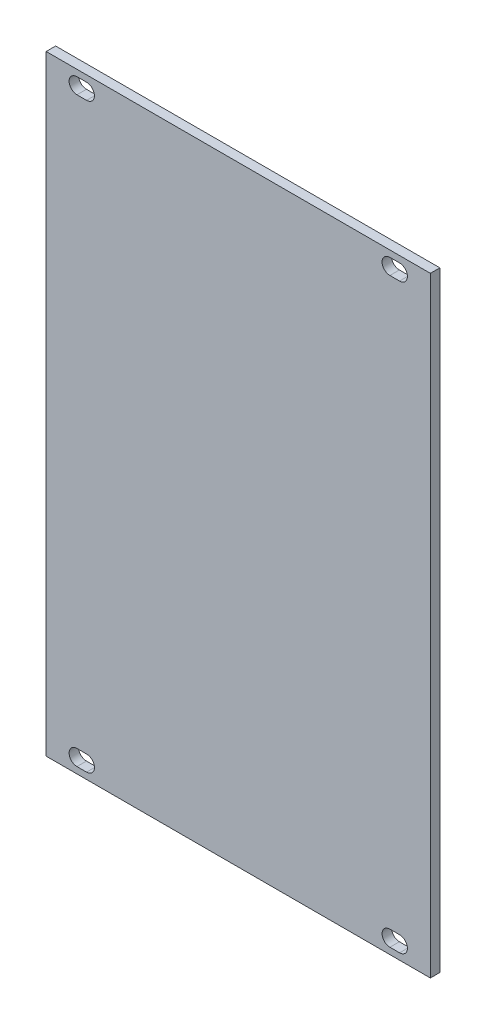
SolidWorks part; units mm, degrees
ref_plane "Front Plane" through (0, 0, 0) normal (0, 0, 1) x (1, 0, 0)
ref_plane "Top Plane" through (0, 0, 0) normal (0, 1, 0) x (1, 0, 0)
ref_plane "Right Plane" through (0, 0, 0) normal (1, 0, 0) x (0, 0, -1)
sketch "Sketch1" plane through (0, 0, 0) normal (0, 0, 1) x (1, 0, 0)
  line L0 (-32.95, 64.25) -> (-32.95, -64.25) construction
  line L1 (-40.45, 64.25) -> (40.45, 64.25)
  line L2 (-40.45, 64.25) -> (-40.45, -64.25)
  line L3 (-40.45, -64.25) -> (40.45, -64.25)
  line L4 (40.45, 64.25) -> (40.45, -64.25)
  line L5 (-40.45, 64.25) -> (40.45, -64.25) construction
  line L6 (-40.45, -64.25) -> (40.45, 64.25) construction
  line L7 (-40.45, 61.25) -> (40.45, 61.25) construction
  line L8 (-40.45, -61.25) -> (40.45, -61.25) construction
  line L9 (-33.966, -61.25) -> (-31.934, -61.25) construction
  line L10 (31.934, 61.25) -> (33.966, 61.25) construction
  line L11 (-33.966, -59.6) -> (-31.934, -59.6)
  line L12 (-33.966, -62.9) -> (-31.934, -62.9)
  line L13 (-33.966, 61.25) -> (-31.934, 61.25) construction
  line L14 (-33.966, 62.9) -> (-31.934, 62.9)
  line L15 (-33.966, 59.6) -> (-31.934, 59.6)
  line L16 (31.934, 62.9) -> (33.966, 62.9)
  line L17 (31.934, 59.6) -> (33.966, 59.6)
  line L18 (31.934, -61.25) -> (33.966, -61.25) construction
  line L19 (31.934, -59.6) -> (33.966, -59.6)
  line L20 (31.934, -62.9) -> (33.966, -62.9)
  line L21 (32.95, 64.25) -> (32.95, -64.25) construction
  arc A0 (-33.966, -59.6) -> (-33.966, -62.9) centre (-33.966, -61.25) ccw
  arc A1 (-31.934, -62.9) -> (-31.934, -59.6) centre (-31.934, -61.25) ccw
  arc A2 (-33.966, 62.9) -> (-33.966, 59.6) centre (-33.966, 61.25) ccw
  arc A3 (-31.934, 59.6) -> (-31.934, 62.9) centre (-31.934, 61.25) ccw
  arc A4 (31.934, 62.9) -> (31.934, 59.6) centre (31.934, 61.25) ccw
  arc A5 (33.966, 59.6) -> (33.966, 62.9) centre (33.966, 61.25) ccw
  arc A6 (31.934, -59.6) -> (31.934, -62.9) centre (31.934, -61.25) ccw
  arc A7 (33.966, -62.9) -> (33.966, -59.6) centre (33.966, -61.25) ccw
  point P0 (0, 0)
  point P8 (32.95, 61.25)
  point P18 (-32.95, -61.25)
  point P24 (-32.95, 61.25)
  point P34 (32.95, -61.25)
  point P42 (0, 0)
  point P43 (0, 0)
  dimension "D6" = 1.65
  dimension "D7" = 1.65
  dimension "D11" = 1.65
  dimension "D13" = 1.65
  dimension "D1" = 128.5
  dimension "D2" = 80.9
  dimension "D3" = 7.5
  dimension "D4" = 3
  dimension "D8" = 2.032
  dimension "D9" = 2.032
  dimension "D10" = 7.5
  dimension "D12" = 2.032
  dimension "D14" = 2.032
  dimension "D5" = 3
extrude "Boss-Extrude1" add sketch "Sketch1" along normal blind 2
